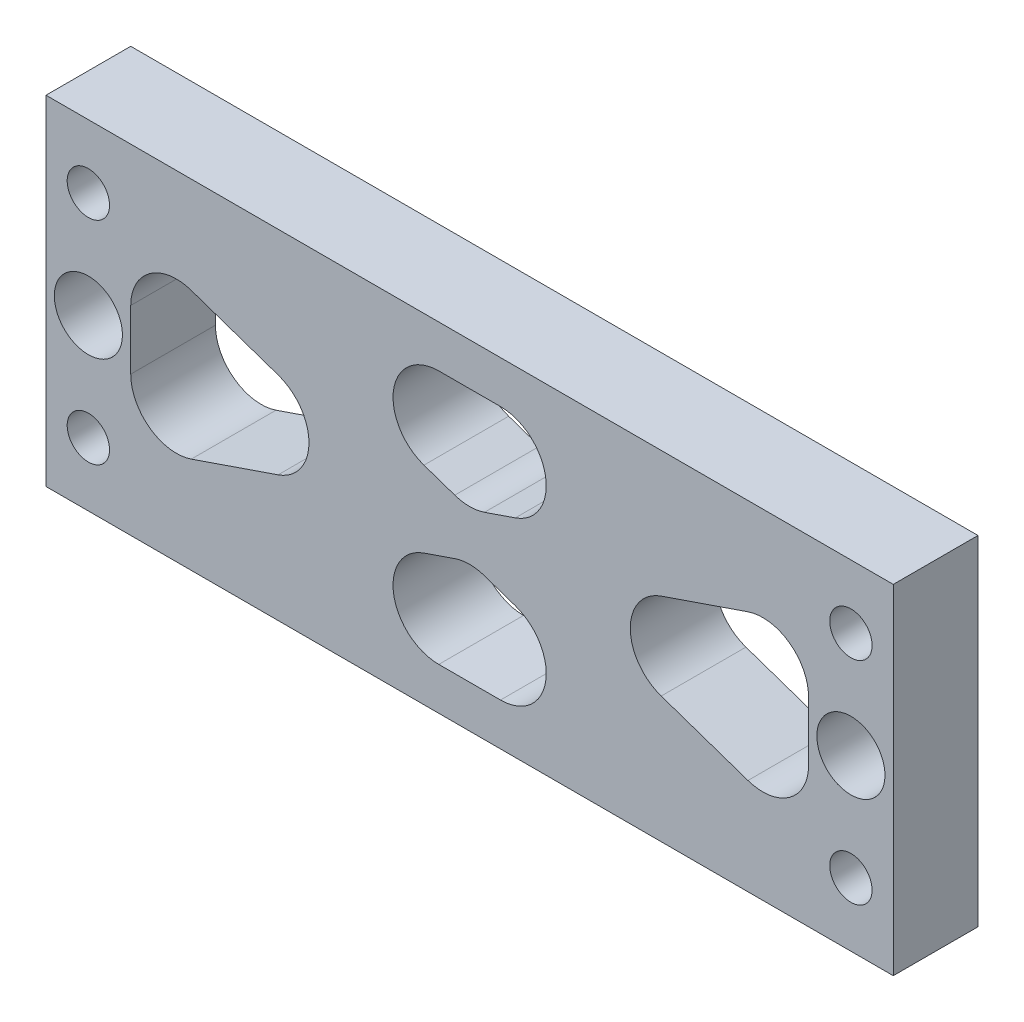
SolidWorks part; units mm, degrees
material "6061-T6 (SS)"
ref_plane "Front Plane" through (0, 0, 0) normal (0, 0, 1) x (1, 0, 0)
ref_plane "Top Plane" through (0, 0, 0) normal (0, 1, 0) x (1, 0, 0)
ref_plane "Right Plane" through (0, 0, 0) normal (1, 0, 0) x (0, 0, -1)
sketch "Sketch1" plane through (0, 0, 0) normal (0, 0, 1) x (1, 0, 0)
  line L1 (-31.75, 12.7) -> (31.75, 12.7)
  line L2 (-31.75, 12.7) -> (-31.75, -12.7)
  line L3 (-31.75, -12.7) -> (31.75, -12.7)
  line L4 (31.75, 12.7) -> (31.75, -12.7)
  line L5 (-31.75, 12.7) -> (31.75, -12.7) construction
  line L6 (-31.75, -12.7) -> (31.75, 12.7) construction
  point P0 (0, 0)
  dimension "D1" = 63.5
  dimension "D2" = 25.4
extrude "Boss-Extrude1" add sketch "Sketch1" along normal blind 6.35
hole_wizard "#10 Clearance Hole1" positions "Sketch2" profile "Sketch3" hole size "#10" standard "ANSI Inch" end condition through all
sketch "Sketch2" plane through (0, 0, 6.35) normal (0, 0, 1) x (1, 0, 0)
  line L0 (-31.75, 12.7) -> (-31.75, -12.7) construction
  line L1 (31.75, -12.7) -> (31.75, 12.7) construction
  point P0 (-28.575, 0)
  point P2 (28.575, 0)
  dimension "D1" = 3.175
  dimension "D2" = 3.175
sketch "Sketch3" plane through (-28.575, 0, 6.35) normal (1, 0, 0) x (0, -1, 0)
  line L0 (0, 0) -> (0, 6.35)
  line L1 (0, 6.35) -> (2.5527, 6.35)
  line L2 (2.5527, 6.35) -> (2.5527, 0)
  line L5 (2.5527, 0) -> (0, 0)
  line L11 (0, -6.35) -> (0, 107.95) construction
  dimension "Thru Hole Dia." = 5.1054
  dimension "Thru Hole Depth" = 6.35
hole_wizard "1/8 (0.125) Transitional Dowel Hole1" positions "Sketch4" profile "Sketch5" hole size "1/8" standard "ANSI Inch" end condition through all
sketch "Sketch4" plane through (0, 0, 6.35) normal (0, 0, 1) x (1, 0, 0)
  line L0 (-28.575, 7.9375) -> (0, 0) construction
  line L1 (0, 0) -> (-28.575, -7.9375) construction
  line L4 (28.575, 7.9375) -> (0, 0) construction
  line L5 (0, 0) -> (28.575, -7.9375) construction
  line L8 (-31.75, 12.7) -> (-31.75, -12.7) construction
  point P0 (-28.575, 7.9375)
  point P2 (-28.575, -7.9375)
  point P4 (28.575, 7.9375)
  point P6 (28.575, -7.9375)
  dimension "D1" = 15.875
  dimension "D2" = 3.175
sketch "Sketch5" plane through (-28.575, 7.9375, 6.35) normal (1, 0, 0) x (0, -1, 0)
  line L0 (0, 0) -> (0, 6.35)
  line L1 (0, 6.35) -> (1.5875, 6.35)
  line L2 (1.5875, 6.35) -> (1.5875, 0)
  line L5 (1.5875, 0) -> (0, 0)
  line L11 (0, -6.35) -> (0, 107.95) construction
  dimension "Thru Hole Dia." = 3.175
  dimension "Thru Hole Depth" = 6.35
sketch "Sketch6" plane through (0, 0, 6.35) normal (0, 0, 1) x (1, 0, 0)
  line L0 (-25.4, 7.0297) -> (-4.8951, 0)
  line L1 (-4.8951, 0) -> (-25.4, -7.0297)
  line L2 (-25.4, -7.0297) -> (-25.4, 7.0297)
  line L3 (-22.8883, 9.525) -> (0, 1.6782)
  line L4 (0, 1.6782) -> (22.8883, 9.525)
  line L5 (22.8883, 9.525) -> (-22.8883, 9.525)
  line L6 (25.4, 7.0297) -> (4.8951, 0)
  line L7 (4.8951, 0) -> (25.4, -7.0297)
  line L8 (25.4, -7.0297) -> (25.4, 7.0297)
  line L9 (22.8883, -9.525) -> (0, -1.6782)
  line L10 (0, -1.6782) -> (-22.8883, -9.525)
  line L11 (-22.8883, -9.525) -> (22.8883, -9.525)
  line L12 (-31.75, -12.7) -> (31.75, -12.7) construction
  line L13 (31.75, 12.7) -> (-31.75, 12.7) construction
  circle A0 centre (-28.575, 0) radius 2.5527 construction
  dimension "D4" = 3.175
  dimension "D1" = 3.175
  dimension "D2" = 3.175
  dimension "D3" = 3.175
extrude "Cut-Extrude1" cut sketch "Sketch6" against normal through all
fillet "Fillet1" radius 3.429 12 edges at (-22.8883, -9.525, 3.175) (0, -1.6782, 3.175) (22.8883, -9.525, 3.175) (25.4, -7.0297, 3.175) (25.4, 7.0297, 3.175) (4.8951, 0, 3.175) (-22.8883, 9.525, 3.175) (22.8883, 9.525, 3.175) (0, 1.6782, 3.175) (-25.4, -7.0297, 3.175) (-4.8951, 0, 3.175) (-25.4, 7.0297, 3.175)
